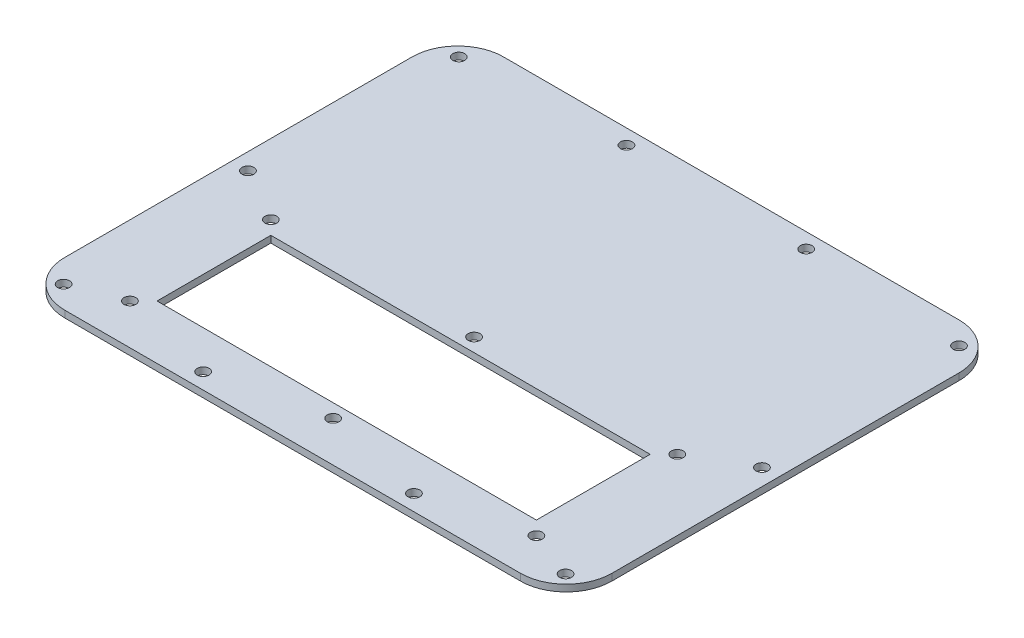
SolidWorks part; units mm, degrees
ref_plane "Front Plane" through (0, 0, 0) normal (0, 0, 1) x (1, 0, 0)
ref_plane "Top Plane" through (0, 0, 0) normal (0, 1, 0) x (1, 0, 0)
ref_plane "Right Plane" through (0, 0, 0) normal (1, 0, 0) x (0, 0, -1)
sketch "Sketch2" plane through (0, 0, 0) normal (0, 1, 0) x (1, 0, 0)
  line L0 (0, 0) -> (0, 207.7092) construction
  line L1 (-106.7689, -102.8065) -> (106.7689, -102.8065)
  line L2 (-128.2065, -81.3689) -> (-128.2065, 81.3689)
  line L3 (-106.7689, 102.8065) -> (106.7689, 102.8065)
  line L4 (128.2065, -81.3689) -> (128.2065, 81.3689)
  line L5 (-128.2065, -102.8065) -> (128.2065, 102.8065) construction
  line L6 (-128.2065, 102.8065) -> (128.2065, -102.8065) construction
  line L7 (0, 207.7092) -> (0, -151.1165) construction
  arc A0 (-106.7689, -102.8065) -> (-128.2065, -81.3689) centre (-106.7689, -81.3689) cw
  arc A1 (106.7689, -102.8065) -> (128.2065, -81.3689) centre (106.7689, -81.3689) ccw
  arc A2 (106.7689, 102.8065) -> (128.2065, 81.3689) centre (106.7689, 81.3689) cw
  arc A3 (-128.2065, 81.3689) -> (-106.7689, 102.8065) centre (-106.7689, 81.3689) cw
  circle A4 centre (42.1132, 95.7453) radius 2.7813
  circle A5 centre (117.221, 92.2909) radius 2.7813
  circle A6 centre (120.4468, -3.3147) radius 2.7813
  circle A7 centre (117.6274, -92.5195) radius 2.7813
  circle A8 centre (49.403, -95.3643) radius 2.7813
  circle A9 centre (-49.403, -95.3643) radius 2.7813
  circle A10 centre (-117.6274, -92.5195) radius 2.7813
  circle A11 centre (-120.4468, -3.3147) radius 2.7813
  circle A12 centre (-117.221, 92.2909) radius 2.7813
  circle A13 centre (-42.1132, 95.7453) radius 2.7813
  point P0 (0, 0)
  dimension "D3" = 21.4376
  dimension "D4" = 5.5626
  dimension "D7" = 5.5626
  dimension "D10" = 5.5626
  dimension "D13" = 5.5626
  dimension "D16" = 5.5626
  dimension "D1" = 205.613
  dimension "D2" = 256.413
  dimension "D5" = 42.1132
  dimension "D6" = 7.0612
  dimension "D8" = 117.221
  dimension "D9" = 10.5156
  dimension "D11" = 120.4468
  dimension "D12" = 106.1212
  dimension "D14" = 195.326
  dimension "D15" = 117.6274
  dimension "D17" = 7.4422
  dimension "D18" = 49.403
extrude "Boss-Extrude1" add sketch "Sketch2" along normal blind 3.175
sketch "Sketch3" plane through (0, 0, 0) normal (0, 1, 0) x (1, 0, 0)
  line L1 (-88.9, -24.13) -> (88.9, -24.13)
  line L2 (-88.9, -24.13) -> (-88.9, -77.47)
  line L3 (-88.9, -77.47) -> (88.9, -77.47)
  line L4 (88.9, -24.13) -> (88.9, -77.47)
  line L5 (-88.9, -24.13) -> (88.9, -77.47) construction
  line L6 (-88.9, -77.47) -> (88.9, -24.13) construction
  point P0 (0, -50.8)
  dimension "D1" = 50.8
  dimension "D2" = 53.34
  dimension "D3" = 177.8
extrude "Cut-Extrude1" cut sketch "Sketch3" along normal blind 3.175
sketch "Sketch4" plane through (0, 0, 0) normal (0, 1, 0) x (1, 0, 0)
  line L0 (-88.9, -24.13) -> (-88.9, -77.47) construction
  line L1 (88.9, -24.13) -> (-88.9, -24.13) construction
  line L2 (88.9, -77.47) -> (88.9, -24.13) construction
  line L3 (-100.8734, -50.8) -> (113.9842, -50.8) construction
  circle A0 centre (-95.25, -17.78) radius 2.7813
  circle A1 centre (0, -17.78) radius 2.7813
  circle A2 centre (95.25, -17.78) radius 2.7813
  circle A3 centre (95.25, -83.82) radius 2.7813
  circle A4 centre (0, -83.82) radius 2.7813
  circle A5 centre (-95.25, -83.82) radius 2.7813
  dimension "D1" = 5.5626
  dimension "D4" = 5.5626
  dimension "D6" = 5.5626
  dimension "D2" = 6.35
  dimension "D3" = 6.35
  dimension "D5" = 6.35
  dimension "D7" = 6.35
  dimension "D8" = 6.35
  dimension "D9" = 26.67
extrude "Cut-Extrude2" cut sketch "Sketch4" along normal blind 3.175
